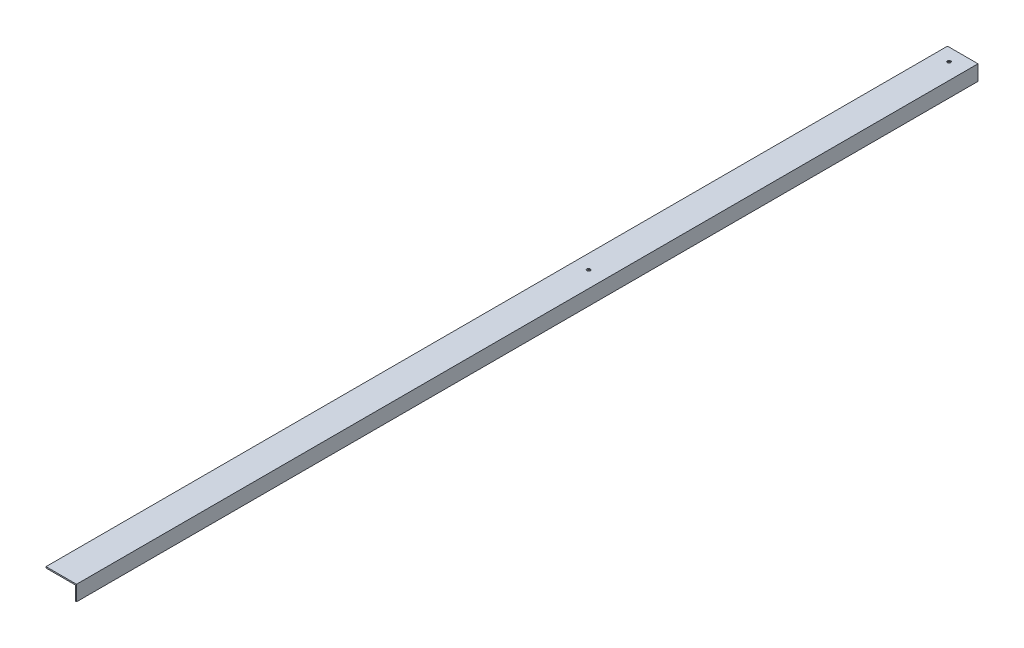
SolidWorks part; units mm, degrees
material "6061-T6 (SS)"
ref_plane "Front Plane" through (0, 0, 0) normal (0, 0, 1) x (1, 0, 0)
ref_plane "Top Plane" through (0, 0, 0) normal (0, 1, 0) x (1, 0, 0)
ref_plane "Right Plane" through (0, 0, 0) normal (1, 0, 0) x (0, 0, -1)
sketch "Sketch1" plane through (0, 0, 0) normal (0, 0, 1) x (1, 0, 0)
  line L0 (-38.1, 0) -> (0, 0)
  line L1 (0, 0) -> (0, -19.05)
  dimension "D1" = 38.1
  dimension "D2" = 19.05
extrude "Extrude-Thin1" add sketch "Sketch1" along normal blind 1125.4359 thin
hole_wizard "#4 Clearance Hole1" positions "Sketch3" profile "Sketch2" hole size "#4" standard "Ansi Inch" end condition up to next
sketch "Sketch3" plane through (0, 0, 0) normal (0, 1, 0) x (-1, 0, 0)
  line L0 (0, 1125.4359) -> (0, 0) construction
  line L1 (38.1, 0) -> (0, 0) construction
  line L2 (20.32, 15.875) -> (20.32, 84.7661) construction
  point P0 (20.32, 15.875)
  point P5 (20.32, 465.875)
  dimension "D1" = 20.32
  dimension "D2" = 15.875
  dimension "D3" = 450
sketch "Sketch2" plane through (-20.32, 0, 15.875) normal (1, 0, 0) x (0, 0, 1)
  line L0 (0, 0) -> (0, 1.5748)
  line L1 (0, 1.5748) -> (2.1082, 1.5748)
  line L2 (1.4732, 0.9398) -> (1.4732, 0.635)
  line L3 (1.4732, 0.635) -> (2.1082, 0)
  line L5 (2.1082, 0) -> (0, 0)
  line L6 (-1.4732, 0.635) -> (-2.1082, 0) construction
  line L7 (2.1082, 1.5748) -> (1.4732, 0.9398)
  line L8 (-2.1082, 1.5748) -> (-1.4732, 0.9398) construction
  line L11 (0, -6.35) -> (0, 107.95) construction
  dimension "Thru Hole Dia." = 2.9464
  dimension "Thru Hole Depth" = 1.5748
  dimension "Near C'Sink Dia." = 4.2164
  dimension "Near C'Sink Angle" = 90
  dimension "Far C'Sink Dia." = 4.2164
  dimension "Far C'Sink Angle" = 90
